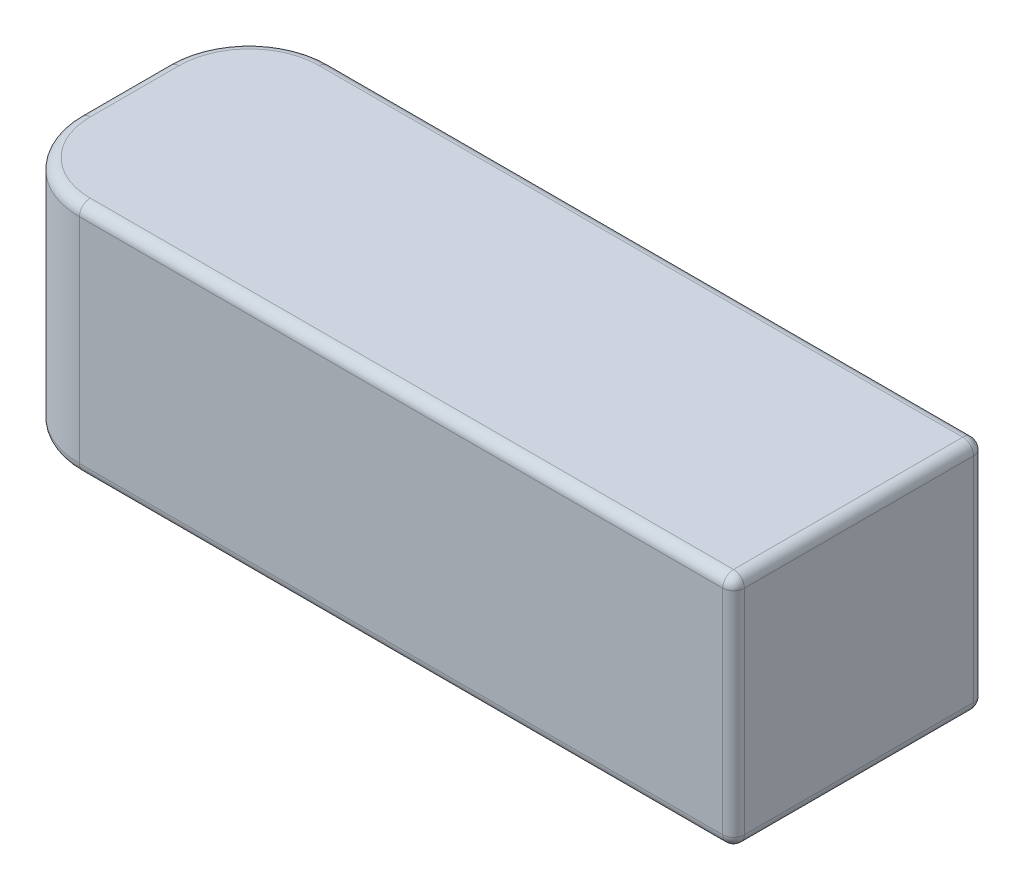
SolidWorks part; units mm, degrees
material "Melamine resin"
ref_plane "Front Plane" through (0, 0, 0) normal (0, 0, 1) x (1, 0, 0)
ref_plane "Top Plane" through (0, 0, 0) normal (0, 1, 0) x (1, 0, 0)
ref_plane "Right Plane" through (0, 0, 0) normal (1, 0, 0) x (0, 0, -1)
sketch "Sketch1" plane through (0, 0, 0) normal (0, 1, 0) x (1, 0, 0)
  line L1 (-68, 23.2) -> (68, 23.2)
  line L2 (-68, 23.2) -> (-68, -23.2)
  line L3 (-68, -23.2) -> (68, -23.2)
  line L4 (68, 23.2) -> (68, -23.2)
  line L5 (-68, 23.2) -> (68, -23.2) construction
  line L6 (-68, -23.2) -> (68, 23.2) construction
  point P0 (0, 0)
  dimension "D1" = 46.4
  dimension "D2" = 136
extrude "Boss-Extrude1" add sketch "Sketch1" along normal blind 43.5
fillet "Fillet1" radius 15 2 edges at (-68, 21.75, -23.2) (-68, 21.75, 23.2)
fillet "Fillet2" radius 2 14 edges at (68, 21.75, 23.2) (68, 21.75, -23.2) (68, 43.5, 0) (7.5, 43.5, 23.2) (-63.6066, 43.5, 18.8066) (-68, 43.5, 0) (-63.6066, 43.5, -18.8066) (7.5, 43.5, -23.2) (-63.6066, 0, 18.8066) (7.5, 0, 23.2) (68, 0, 0) (7.5, 0, -23.2) (-63.6066, 0, -18.8066) (-68, 0, 0)
